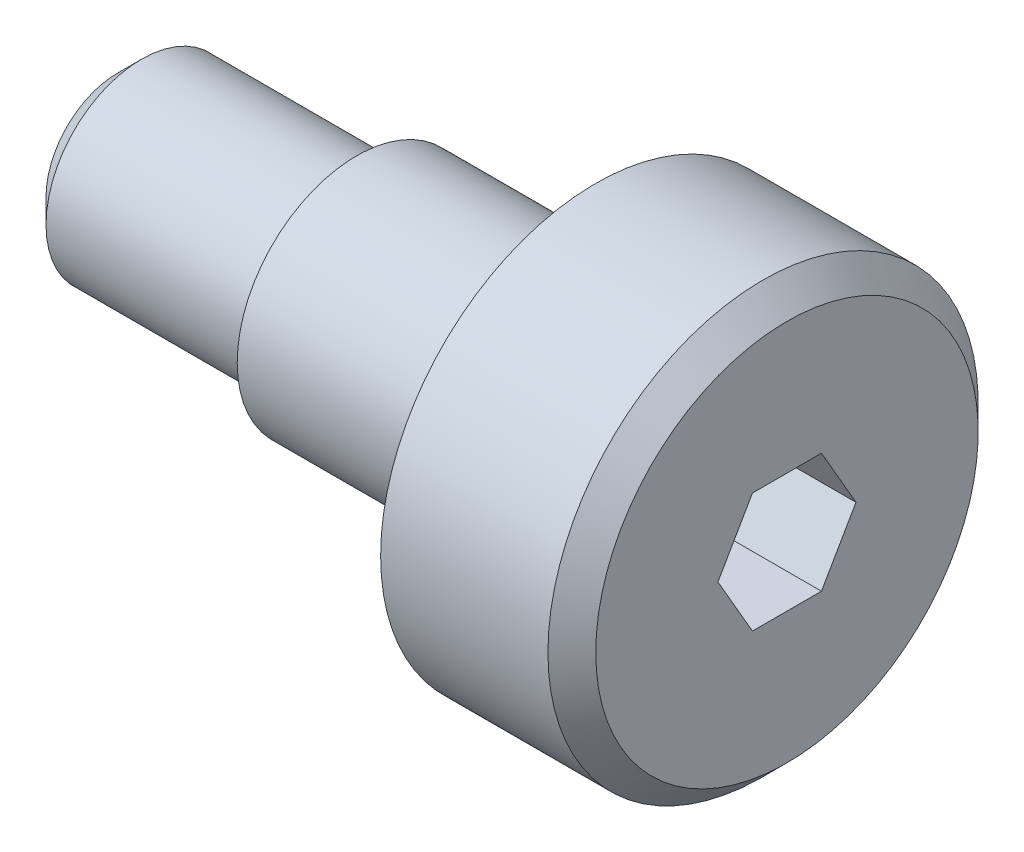
SolidWorks part; units mm, degrees
material "AISI Type 316L stainless steel"
ref_plane "Front Plane" through (0, 0, 0) normal (0, 0, 1) x (1, 0, 0)
ref_plane "Top Plane" through (0, 0, 0) normal (0, 1, 0) x (1, 0, 0)
ref_plane "Right Plane" through (0, 0, 0) normal (1, 0, 0) x (0, 0, -1)
sketch "Sketch1" plane through (0, 0, 0) normal (0, 0, 1) x (1, 0, 0)
  line L0 (0, 0) -> (14, 0)
  line L1 (14, 0) -> (14, 4)
  line L2 (13.5, 4.5) -> (10, 4.5)
  line L3 (10, 4.5) -> (10, 2.5)
  line L4 (10, 2.5) -> (5, 2.5)
  line L5 (5, 2.5) -> (5, 2)
  line L6 (5, 2) -> (0.5, 2)
  line L7 (0, 1.5) -> (0, 0)
  line L8 (0.5, 2) -> (0, 1.5)
  line L9 (14, 4) -> (13.5, 4.5)
  point P4 (14, 4.5)
  point P9 (0, 2)
  dimension "D1" = 5
  dimension "D2" = 2
  dimension "D3" = 5
  dimension "D4" = 2.5
  dimension "D5" = 4
  dimension "D6" = 4.5
revolve "Revolve1" add sketch "Sketch1" angle 360 about L0
sketch "Sketch2" plane through (14, 0, 0) normal (1, 0, 0) x (0, 0, -1)
  line L1 (1.4434, 0) -> (0.7217, 1.25)
  line L2 (0.7217, 1.25) -> (-0.7217, 1.25)
  line L3 (-0.7217, 1.25) -> (-1.4434, 0)
  line L4 (-1.4434, 0) -> (-0.7217, -1.25)
  line L5 (-0.7217, -1.25) -> (0.7217, -1.25)
  line L6 (0.7217, -1.25) -> (1.4434, 0)
  circle A0 centre (0, 0) radius 1.25 construction
  dimension "D1" = 2.5
extrude "Cut-Extrude1" cut sketch "Sketch2" against normal blind 4
